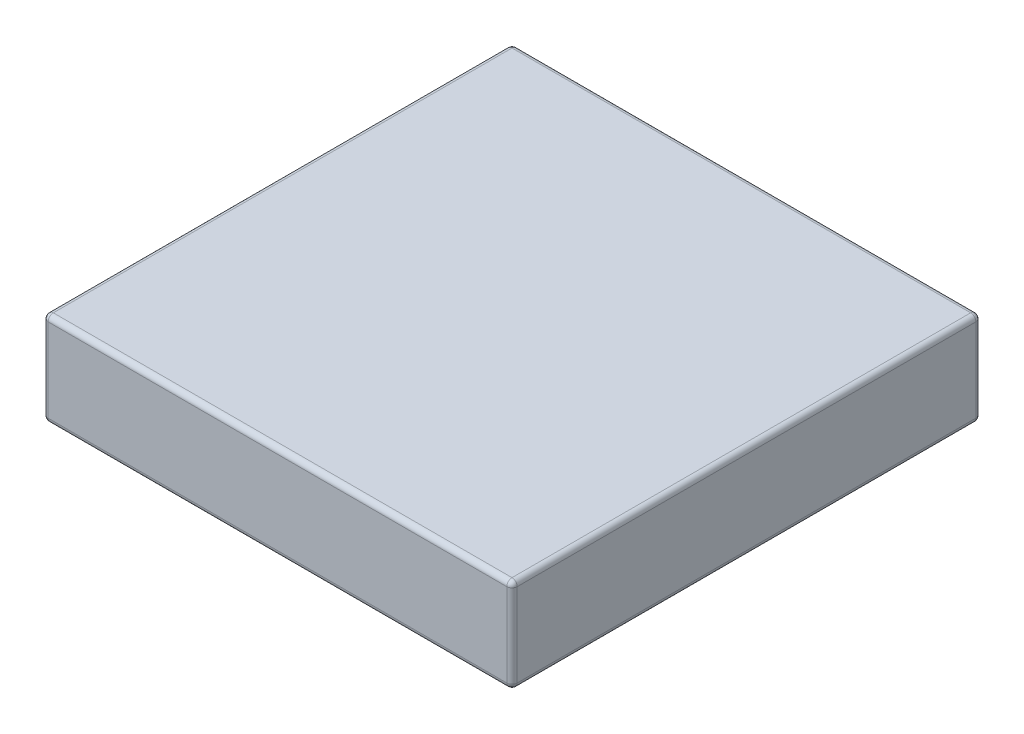
SolidWorks part; units mm, degrees
ref_plane "Front Plane" through (0, 0, 0) normal (0, 0, 1) x (1, 0, 0)
ref_plane "Top Plane" through (0, 0, 0) normal (0, 1, 0) x (1, 0, 0)
ref_plane "Right Plane" through (0, 0, 0) normal (1, 0, 0) x (0, 0, -1)
sketch "Sketch1" plane through (0, 0, 0) normal (0, 1, 0) x (1, 0, 0)
  line L1 (0, 0) -> (90, 0)
  line L2 (0, 0) -> (0, 90)
  line L3 (0, 90) -> (90, 90)
  line L4 (90, 0) -> (90, 90)
  dimension "D1" = 90
  dimension "D2" = 90
extrude "Boss-Extrude1" add sketch "Sketch1" along normal blind 18
fillet "Fillet1" radius 1 12 edges at (0, 9, 0) (90, 9, 0) (90, 9, -90) (0, 9, -90) (45, 18, -90) (90, 18, -45) (45, 18, 0) (0, 18, -45) (45, 0, 0) (90, 0, -45) (45, 0, -90) (0, 0, -45)
sketch "Sketch5" plane through (0, 18, 0) normal (0, 1, 0) x (1, 0, 0)
  line L0 (1, 89) -> (89, 1) construction
  text T0 "nikon T2 lens converter" font "Arial Narrow" height in points 28
extrude "Boss-Extrude2" add sketch "Sketch5" against normal offset from surface (2 mm away) 2 up to face at (45, 18, -45)
